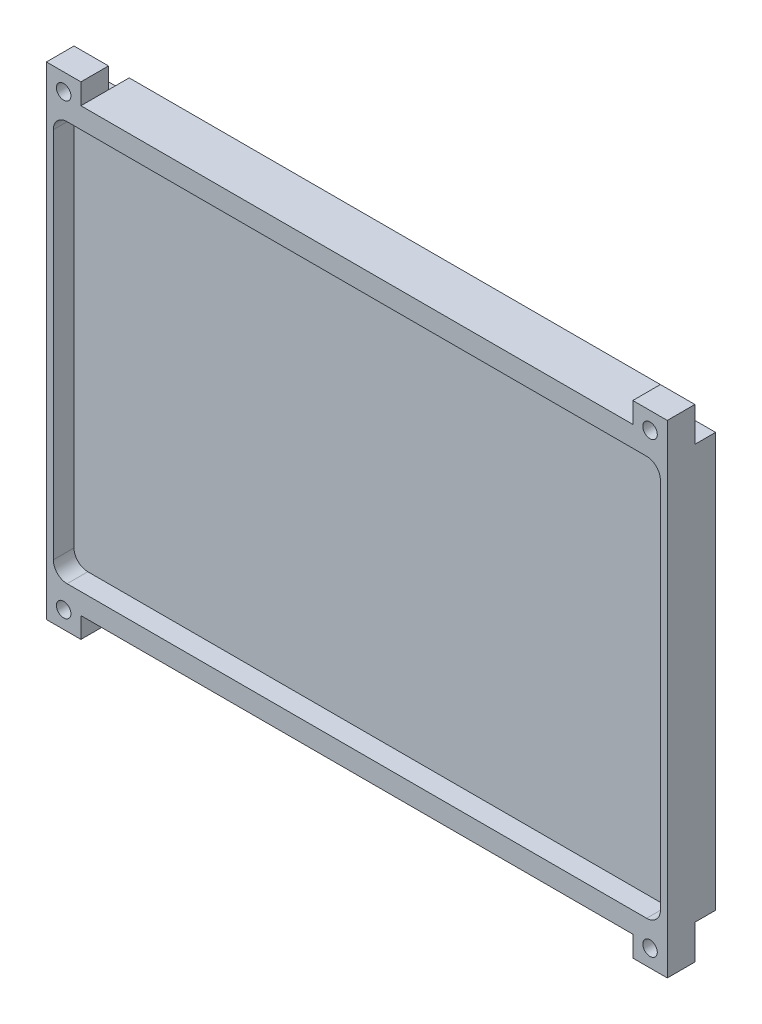
SolidWorks part; units mm, degrees
ref_plane "前基準面" through (0, 0, 0) normal (0, 0, 1) x (1, 0, 0)
ref_plane "上基準面" through (0, 0, 0) normal (0, 1, 0) x (1, 0, 0)
ref_plane "右基準面" through (0, 0, 0) normal (1, 0, 0) x (0, 0, -1)
sketch "草圖1" plane through (0, 0, 0) normal (0, 0, 1) x (1, 0, 0)
  line L1 (-89.0867, 42.9814) -> (10.9133, 42.9814)
  line L2 (-89.0867, 42.9814) -> (-89.0867, -27.0186)
  line L3 (-89.0867, -27.0186) -> (10.9133, -27.0186)
  line L4 (10.9133, 42.9814) -> (10.9133, -27.0186)
  dimension "D1" = 70
  dimension "D2" = 100
extrude "填料-伸長1" add sketch "草圖1" along normal blind 10 contours L4 L3 L2 L1
ref_plane "平面1" through (0, 0, 10) normal (0, 0, 1) x (1, 0, 0)
sketch "草圖6" plane through (0, 0, 10) normal (0, 0, 1) x (1, 0, 0)
  line L0 (-89.0867, 7.9814) -> (10.9133, 7.9814) construction
  line L1 (-89.0867, 42.9814) -> (-89.0867, -27.0186) construction
  line L2 (10.9133, 42.9814) -> (10.9133, -27.0186) construction
  line L3 (-39.0867, 42.9814) -> (-39.0867, -27.0186) construction
  line L4 (-89.0867, 42.9814) -> (10.9133, 42.9814) construction
  line L5 (-89.0867, -27.0186) -> (10.9133, -27.0186) construction
  line L6 (5.9133, 37.9814) -> (0.9133, 37.9814)
  line L7 (-84.0867, 42.9814) -> (-79.0867, 42.9814)
  line L8 (-84.0867, 42.9814) -> (-84.0867, 37.9814)
  line L9 (-84.0867, 37.9814) -> (-79.0867, 37.9814)
  line L10 (-79.0867, 42.9814) -> (-79.0867, 37.9814)
  line L11 (0.9133, 42.9814) -> (0.9133, 37.9814)
  line L12 (5.9133, 42.9814) -> (0.9133, 42.9814)
  line L13 (5.9133, 42.9814) -> (5.9133, 37.9814)
  line L14 (-84.0867, -22.0186) -> (-79.0867, -22.0186)
  line L15 (-79.0867, -27.0186) -> (-79.0867, -22.0186)
  line L16 (-84.0867, -27.0186) -> (-79.0867, -27.0186)
  line L17 (-84.0867, -27.0186) -> (-84.0867, -22.0186)
  line L18 (5.9133, -27.0186) -> (5.9133, -22.0186)
  line L19 (5.9133, -27.0186) -> (0.9133, -27.0186)
  line L20 (0.9133, -27.0186) -> (0.9133, -22.0186)
  line L21 (5.9133, -22.0186) -> (0.9133, -22.0186)
  dimension "D1" = 5
  dimension "D2" = 5
  dimension "D3" = 5
extrude "除料-伸長4" cut sketch "草圖6" against normal blind 5
ref_plane "平面2" through (0, 0, 0) normal (0, 0, -1) x (-1, 0, 0)
sketch "草圖7" plane through (0, 0, 0) normal (0, 0, -1) x (-1, 0, 0)
  line L0 (-10.9133, 7.9814) -> (89.0867, 7.9814) construction
  line L1 (-10.9133, 42.9814) -> (-10.9133, -27.0186) construction
  line L2 (89.0867, 42.9814) -> (89.0867, -27.0186) construction
  line L3 (39.0867, 42.9814) -> (39.0867, -27.0186) construction
  line L4 (89.0867, 42.9814) -> (-10.9133, 42.9814) construction
  line L5 (89.0867, -27.0186) -> (-10.9133, -27.0186) construction
  line L6 (84.0867, 37.9814) -> (79.0867, 37.9814)
  line L7 (-5.9133, 42.9814) -> (-0.9133, 42.9814)
  line L8 (-5.9133, 42.9814) -> (-5.9133, 37.9814)
  line L9 (-5.9133, 37.9814) -> (-0.9133, 37.9814)
  line L10 (-0.9133, 42.9814) -> (-0.9133, 37.9814)
  line L11 (79.0867, 42.9814) -> (79.0867, 37.9814)
  line L12 (84.0867, 42.9814) -> (79.0867, 42.9814)
  line L13 (84.0867, 42.9814) -> (84.0867, 37.9814)
  line L14 (84.0867, -27.0186) -> (84.0867, -22.0186)
  line L15 (84.0867, -27.0186) -> (79.0867, -27.0186)
  line L16 (79.0867, -27.0186) -> (79.0867, -22.0186)
  line L17 (84.0867, -22.0186) -> (79.0867, -22.0186)
  line L18 (-5.9133, -22.0186) -> (-0.9133, -22.0186)
  line L19 (-0.9133, -27.0186) -> (-0.9133, -22.0186)
  line L20 (-5.9133, -27.0186) -> (-0.9133, -27.0186)
  line L21 (-5.9133, -27.0186) -> (-5.9133, -22.0186)
  dimension "D1" = 5
  dimension "D2" = 5
  dimension "D3" = 5
extrude "除料-伸長5" cut sketch "草圖7" against normal blind 3
sketch "草圖8" plane through (0, 0, 0) normal (0, 0, -1) x (-1, 0, 0)
  line L0 (-10.9133, 7.9814) -> (89.0867, 7.9814) construction
  line L1 (-10.9133, 42.9814) -> (-10.9133, -27.0186) construction
  line L2 (89.0867, 42.9814) -> (89.0867, -27.0186) construction
  line L3 (39.0867, 42.9814) -> (39.0867, -27.0186) construction
  line L4 (79.0867, 42.9814) -> (-0.9133, 42.9814) construction
  line L5 (79.0867, -27.0186) -> (-0.9133, -27.0186) construction
  line L6 (-5.9133, 40.4814) -> (-0.9133, 40.4814) construction
  line L7 (-5.9133, 42.9814) -> (-5.9133, 37.9814) construction
  line L8 (-0.9133, 37.9814) -> (-0.9133, 42.9814) construction
  line L9 (-3.4133, 37.9814) -> (-3.4133, 42.9814) construction
  line L10 (-5.9133, 37.9814) -> (-0.9133, 37.9814) construction
  line L11 (-0.9133, 42.9814) -> (-5.9133, 42.9814) construction
  circle A0 centre (-3.4133, 40.4814) radius 1.05
  circle A1 centre (81.5867, 40.4814) radius 1.05
  circle A2 centre (81.5867, -24.5186) radius 1.05
  circle A3 centre (-3.4133, -24.5186) radius 1.05
  dimension "D1" = 2.1
  dimension "D2" = 2.1
  dimension "D3" = 2.1
  dimension "D4" = 2.1
extrude "除料-伸長6" cut sketch "草圖8" against normal blind 42
sketch "草圖10" plane through (0, 0, 0) normal (0, 0, 1) x (1, 0, 0)
  line L1 (-89.0867, 42.9814) -> (10.9133, 42.9814)
  line L2 (-89.0867, 42.9814) -> (-89.0867, -27.0186)
  line L3 (-89.0867, -27.0186) -> (10.9133, -27.0186)
  line L4 (10.9133, 42.9814) -> (10.9133, -27.0186)
extrude "除料-伸長7" cut sketch "草圖10" along normal blind 3
ref_plane "平面3" through (10.9133, 0, 0) normal (1, 0, 0) x (0, 0, -1)
sketch "草圖11" plane through (10.9133, 0, 0) normal (1, 0, 0) x (0, 0, -1)
  line L0 (-10, 38.5) -> (-10, -38.5) construction
  line L1 (-3, 42.9814) -> (-10, 42.9814)
  line L2 (-3, 42.9814) -> (-3, -27.0186)
  line L3 (-3, -27.0186) -> (-10, -27.0186)
  line L4 (-10, 42.9814) -> (-10, -27.0186)
  line L5 (-10, -27.0186) -> (-3, -27.0186) construction
extrude "除料-伸長8" cut sketch "草圖11" against normal blind 5
ref_plane "平面4" through (-89.0867, 0, 0) normal (-1, 0, 0) x (0, 0, 1)
sketch "草圖12" plane through (-89.0867, 0, 0) normal (-1, 0, 0) x (0, 0, 1)
  line L1 (3, 42.9814) -> (10, 42.9814)
  line L2 (3, 42.9814) -> (3, -27.0186)
  line L3 (3, -27.0186) -> (10, -27.0186)
  line L4 (10, 42.9814) -> (10, -27.0186)
extrude "除料-伸長9" cut sketch "草圖12" against normal blind 5
ref_plane "平面5" through (0, 0, 10) normal (0, 0, 1) x (1, 0, 0)
sketch "草圖13" plane through (0, 0, 10) normal (0, 0, 1) x (1, 0, 0)
  line L0 (-39.0867, 42.9814) -> (-39.0867, -27.0186) construction
  line L1 (-84.0867, 37.9814) -> (-79.0867, 37.9814)
  line L2 (-84.0867, 37.9814) -> (-84.0867, -22.0186)
  line L3 (-84.0867, -22.0186) -> (-79.0867, -22.0186)
  line L4 (-79.0867, 37.9814) -> (-79.0867, -22.0186)
  line L5 (-79.0867, 42.9814) -> (0.9133, 42.9814) construction
  line L6 (-79.0867, -27.0186) -> (0.9133, -27.0186) construction
  line L7 (5.9133, -22.0186) -> (0.9133, -22.0186)
  line L8 (0.9133, 37.9814) -> (0.9133, -22.0186)
  line L9 (5.9133, 37.9814) -> (0.9133, 37.9814)
  line L10 (5.9133, 37.9814) -> (5.9133, -22.0186)
sketch "草圖15" plane through (0, 0, 10) normal (0, 0, 1) x (1, 0, 0)
  line L0 (-84.0867, 7.9814) -> (0.9133, 7.9814) construction
  line L1 (-84.0867, 37.9814) -> (-84.0867, -22.0186) construction
  line L2 (0.9133, 37.9814) -> (0.9133, -22.0186) construction
  line L3 (-39.0867, 42.9814) -> (-39.0867, -27.0186) construction
  line L24 (-83.0867, 34.9814) -> (-83.0867, -19.0186)
  line L25 (-81.0867, 36.9814) -> (2.9133, 36.9814)
  line L26 (4.9133, 34.9814) -> (4.9133, -19.0186)
  line L27 (-80.0867, 33.9814) -> (1.9133, 33.9814)
  line L28 (-79.0867, 42.9814) -> (0.9133, 42.9814) construction
  line L29 (5.9133, 37.9814) -> (5.9133, -22.0186) construction
  line L30 (-80.0867, 33.9814) -> (-80.0867, -18.0186)
  line L31 (1.9133, 33.9814) -> (1.9133, -18.0186)
  line L32 (-81.0867, -21.0186) -> (2.9133, -21.0186)
  line L33 (-80.0867, -18.0186) -> (1.9133, -18.0186)
  arc A0 (-81.0867, -21.0186) -> (-83.0867, -19.0186) centre (-81.0867, -19.0186) cw
  arc A1 (2.9133, -21.0186) -> (4.9133, -19.0186) centre (2.9133, -19.0186) ccw
  arc A2 (-83.0867, 34.9814) -> (-81.0867, 36.9814) centre (-81.0867, 34.9814) cw
  arc A3 (2.9133, 36.9814) -> (4.9133, 34.9814) centre (2.9133, 34.9814) cw
  point P19 (-83.0867, 7.9814)
  point P21 (-83.0867, -21.0186)
  point P26 (-0.0867, 7.9814)
  point P27 (1.9133, 7.9814)
  point P29 (-80.0867, 7.9814)
  point P30 (-83.0867, 7.9814)
  point P31 (4.9133, -21.0186)
  point P32 (4.9133, 7.9814)
  point P33 (1.9133, 7.9814)
  point P35 (-80.0867, 7.9814)
  point P38 (-83.0867, 36.9814)
  point P41 (4.9133, 36.9814)
  dimension "D8" = 2
  dimension "D1" = 3
  dimension "D2" = 9
  dimension "D3" = 3
  dimension "D4" = 1
  dimension "D5" = 1
  dimension "D6" = 3
  dimension "D7" = 6
extrude "除料-伸長12" cut sketch "草圖15" against normal blind 3
ref_plane "平面6" through (0, 0, 5) normal (0, 0, 1) x (1, 0, 0)
sketch "草圖16" plane through (0, 0, 5) normal (0, 0, 1) x (1, 0, 0)
  line L0 (-84.0867, 7.9814) -> (0.9133, 7.9814) construction
  line L1 (-84.0867, 37.9814) -> (-84.0867, -22.0186) construction
  line L2 (0.9133, 37.9814) -> (0.9133, -22.0186) construction
  line L3 (-39.0867, 42.9814) -> (-39.0867, -27.0186) construction
  line L4 (-84.0867, 42.9814) -> (-84.0867, 37.9814) construction
  line L5 (-79.0867, 37.9814) -> (-84.0867, 37.9814)
  line L6 (-79.0867, 37.9814) -> (-79.0867, 42.9814)
  line L7 (-79.0867, 42.9814) -> (-84.0867, 42.9814)
  line L8 (-84.0867, 37.9814) -> (-84.0867, 42.9814)
  line L9 (0.9133, 42.9814) -> (5.9133, 42.9814)
  line L10 (5.9133, 37.9814) -> (5.9133, 42.9814)
  line L11 (0.9133, 37.9814) -> (5.9133, 37.9814)
  line L12 (0.9133, 37.9814) -> (0.9133, 42.9814)
  line L13 (0.9133, -22.0186) -> (0.9133, -27.0186)
  line L14 (0.9133, -22.0186) -> (5.9133, -22.0186)
  line L15 (5.9133, -22.0186) -> (5.9133, -27.0186)
  line L16 (0.9133, -27.0186) -> (5.9133, -27.0186)
  line L17 (-79.0867, -27.0186) -> (-84.0867, -27.0186)
  line L18 (-84.0867, -22.0186) -> (-84.0867, -27.0186)
  line L19 (-79.0867, -22.0186) -> (-84.0867, -22.0186)
  line L20 (-79.0867, -22.0186) -> (-79.0867, -27.0186)
  circle A0 centre (-81.5867, 40.4814) radius 1.05
  circle A1 centre (3.4133, 40.4814) radius 1.05
  circle A2 centre (3.4133, -24.5186) radius 1.05
  circle A3 centre (-81.5867, -24.5186) radius 1.05
extrude "填料-伸長2" add sketch "草圖16" along normal blind 5
sketch "草圖18" plane through (0, 0, 10) normal (0, 0, 1) x (1, 0, 0)
  line L0 (-84.0867, 7.9814) -> (5.9133, 7.9814) construction
  line L1 (-84.0867, 37.9814) -> (-84.0867, -22.0186) construction
  line L2 (5.9133, 37.9814) -> (5.9133, -22.0186) construction
  line L3 (-84.0867, 42.9814) -> (5.9133, 42.9814) construction
  line L4 (-79.0867, 42.9814) -> (0.9133, 42.9814)
  line L5 (-79.0867, 42.9814) -> (-79.0867, 39.9814)
  line L6 (-79.0867, 39.9814) -> (0.9133, 39.9814)
  line L7 (0.9133, 42.9814) -> (0.9133, 39.9814)
  line L8 (2.9133, 36.9814) -> (-81.0867, 36.9814) construction
  line L9 (-79.0867, -24.0186) -> (0.9133, -24.0186)
  line L10 (0.9133, -27.0186) -> (0.9133, -24.0186)
  line L11 (-79.0867, -27.0186) -> (0.9133, -27.0186)
  line L12 (-79.0867, -27.0186) -> (-79.0867, -24.0186)
  dimension "D1" = 80
  dimension "D2" = 5
  dimension "D3" = 5
  dimension "D4" = 3
extrude "除料-伸長13" cut sketch "草圖18" against normal blind 10
sketch "草圖19" plane through (0, 0, 10) normal (0, 0, 1) x (1, 0, 0)
  line L1 (-80.0867, 33.9814) -> (1.9133, 33.9814)
  line L2 (-80.0867, 33.9814) -> (-80.0867, -18.0186)
  line L3 (-80.0867, -18.0186) -> (1.9133, -18.0186)
  line L4 (1.9133, 33.9814) -> (1.9133, -18.0186)
extrude "除料-伸長14" cut sketch "草圖19" against normal blind 3
ref_plane "平面7" through (0, 0, 3) normal (0, 0, -1) x (-1, 0, 0)
sketch "草圖20" plane through (0, 0, 3) normal (0, 0, -1) x (-1, 0, 0)
  line L0 (-5.9133, 7.9814) -> (84.0867, 7.9814) construction
  line L1 (-5.9133, 37.9814) -> (-5.9133, -22.0186) construction
  line L2 (84.0867, 37.9814) -> (84.0867, -22.0186) construction
  line L3 (39.0867, 42.9814) -> (39.0867, -27.0186) construction
  line L4 (79.0867, 42.9814) -> (79.0867, 37.9814)
  line L5 (-5.9133, 42.9814) -> (-0.9133, 42.9814)
  line L6 (-5.9133, 42.9814) -> (-5.9133, 37.9814)
  line L7 (-5.9133, 37.9814) -> (-0.9133, 37.9814)
  line L8 (-0.9133, 42.9814) -> (-0.9133, 37.9814)
  line L9 (84.0867, 42.9814) -> (79.0867, 42.9814)
  line L10 (84.0867, 42.9814) -> (84.0867, 37.9814)
  line L11 (84.0867, 37.9814) -> (79.0867, 37.9814)
  line L12 (84.0867, -27.0186) -> (79.0867, -27.0186)
  line L13 (84.0867, -27.0186) -> (84.0867, -22.0186)
  line L14 (84.0867, -22.0186) -> (79.0867, -22.0186)
  line L15 (79.0867, -27.0186) -> (79.0867, -22.0186)
  line L16 (-0.9133, -27.0186) -> (-0.9133, -22.0186)
  line L17 (-5.9133, -27.0186) -> (-0.9133, -27.0186)
  line L18 (-5.9133, -27.0186) -> (-5.9133, -22.0186)
  line L19 (-5.9133, -22.0186) -> (-0.9133, -22.0186)
extrude "除料-伸長15" cut sketch "草圖20" against normal blind 3
